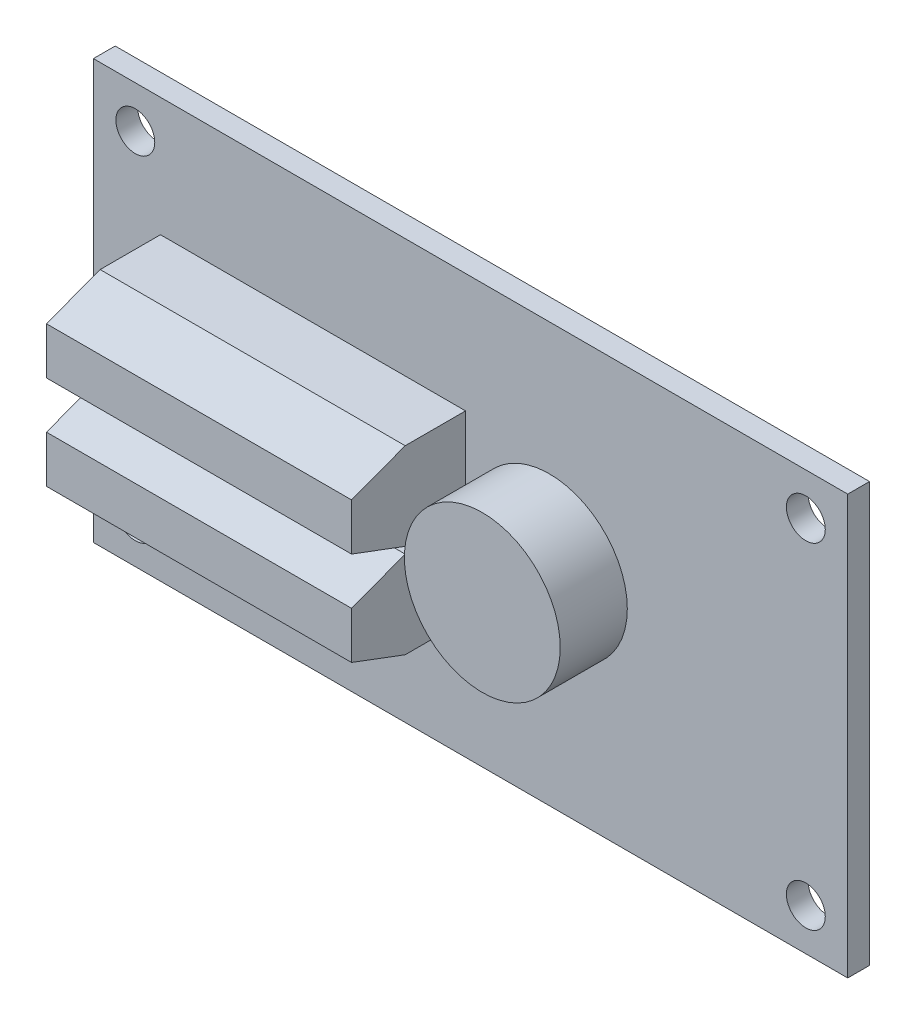
SolidWorks part; units mm, degrees
ref_plane "Front Plane" through (0, 0, 0) normal (0, 0, 1) x (1, 0, 0)
ref_plane "Top Plane" through (0, 0, 0) normal (0, 1, 0) x (1, 0, 0)
ref_plane "Right Plane" through (0, 0, 0) normal (1, 0, 0) x (0, 0, -1)
sketch "Sketch1" plane through (0, 0, 0) normal (0, 0, 1) x (1, 0, 0)
  line L1 (-28.575, 15.875) -> (28.575, 15.875)
  line L2 (-28.575, 15.875) -> (-28.575, -15.875)
  line L3 (-28.575, -15.875) -> (28.575, -15.875)
  line L4 (28.575, 15.875) -> (28.575, -15.875)
  line L5 (-28.575, 15.875) -> (28.575, -15.875) construction
  line L6 (-28.575, -15.875) -> (28.575, 15.875) construction
  point P0 (0, 0)
  dimension "D1" = 57.15
  dimension "D2" = 31.75
extrude "Boss-Extrude1" add sketch "Sketch1" along normal blind 1.651
sketch "Sketch2" plane through (0, 0, 1.651) normal (0, 0, 1) x (1, 0, 0)
  line L0 (25.4, 15.875) -> (25.4, -15.875) construction
  line L1 (28.575, 15.875) -> (-28.575, 15.875) construction
  line L2 (-28.575, -15.875) -> (28.575, -15.875) construction
  line L3 (-25.4, 15.875) -> (-25.4, -15.875) construction
  line L4 (-28.575, 12.7) -> (28.575, 12.7) construction
  line L5 (-28.575, 15.875) -> (-28.575, -15.875) construction
  line L6 (28.575, -15.875) -> (28.575, 15.875) construction
  line L7 (-28.575, -12.7) -> (28.575, -12.7) construction
  circle A0 centre (25.4, -12.7) radius 1.4732
  circle A1 centre (25.4, 12.7) radius 1.4732
  circle A2 centre (-25.4, 12.7) radius 1.4732
  circle A3 centre (-25.4, -12.7) radius 1.4732
  dimension "D1" = 2.9464
  dimension "D2" = 3.175
  dimension "D3" = 3.175
  dimension "D4" = 3.175
  dimension "D5" = 3.175
extrude "Mount-Holes" cut sketch "Sketch2" against normal through all
sketch "Sketch3" plane through (0, 0, 1.651) normal (0, 0, 1) x (1, 0, 0)
  line L0 (0, 0) -> (-28.575, 0) construction
  line L1 (-28.575, 15.875) -> (-28.575, -15.875) construction
  line L3 (-23.495, -0.254) -> (-0.381, -0.254)
  line L4 (-23.495, -0.254) -> (-23.495, -6.858)
  line L5 (-23.495, -6.858) -> (-0.381, -6.858)
  line L6 (-0.381, -0.254) -> (-0.381, -6.858)
  dimension "D1" = 6.604
  dimension "D2" = 23.114
  dimension "D3" = 5.08
  dimension "D4" = 0.254
extrude "Boss-Extrude2" add sketch "Sketch3" along normal blind 8.636
sketch "Sketch4" plane through (-23.495, 0, 0) normal (-1, 0, 0) x (0, 0, 1)
  line L0 (6.223, -6.858) -> (10.287, -5.334)
  line L1 (10.287, -6.858) -> (1.651, -6.858) construction
  line L2 (10.287, -0.254) -> (10.287, -6.858) construction
  line L3 (6.223, -6.858) -> (10.287, -6.858)
  line L4 (10.287, -6.858) -> (10.287, -5.334)
  line L5 (10.287, -3.556) -> (6.223, -3.556) construction
  line L6 (10.287, -0.254) -> (10.287, -1.778)
  line L7 (6.223, -0.254) -> (10.287, -0.254)
  line L8 (6.223, -0.254) -> (10.287, -1.778)
  dimension "D1" = 4.064
  dimension "D2" = 1.524
extrude "Cut-Extrude1" cut sketch "Sketch4" against normal up to next (23.114 mm away)
mirror "Mirror1" about plane through (0, 0, 0) normal (0, 1, 0) of "Cut-Extrude1", "Boss-Extrude2"
sketch "Sketch5" plane through (0, 0, 0) normal (0, 0, -1) x (-1, 0, 0)
  line L1 (-20.193, 4.953) -> (-10.287, 4.953)
  line L2 (-20.193, 4.953) -> (-20.193, -4.953)
  line L3 (-20.193, -4.953) -> (-10.287, -4.953)
  line L4 (-10.287, 4.953) -> (-10.287, -4.953)
  line L5 (-28.575, -15.875) -> (-28.575, 15.875) construction
  line L6 (-28.575, 0) -> (-24.0213, 0) construction
  point P9 (-20.193, 0)
  dimension "D1" = 9.906
  dimension "D3" = 8.382
extrude "Large bottom chip" add sketch "Sketch5" along normal blind 1.524
sketch "Sketch8" plane through (0, 0, 1.651) normal (0, 0, 1) x (1, 0, 0)
  line L0 (-28.575, 0) -> (1.7823, 0) construction
  line L1 (-28.575, 15.875) -> (-28.575, -15.875) construction
  line L2 (-0.381, -5.334) -> (-0.381, -1.778) construction
  circle A0 centre (5.969, 0) radius 5.9055
  dimension "D1" = 11.811
  dimension "D2" = 6.35
extrude "Buzzer" add sketch "Sketch8" along normal blind 5.08
sketch "Sketch9" plane through (0, 0, 0) normal (0, 0, -1) x (-1, 0, 0)
  line L0 (28.575, -15.875) -> (-28.575, -15.875) construction
  line L1 (-4.445, -9.906) -> (3.175, -9.906)
  line L2 (-4.445, -9.906) -> (-4.445, -15.748)
  line L3 (-4.445, -15.748) -> (3.175, -15.748)
  line L4 (3.175, -9.906) -> (3.175, -15.748)
  line L5 (-28.575, -15.875) -> (-28.575, 15.875) construction
  dimension "D1" = 7.62
  dimension "D2" = 5.842
  dimension "D3" = 0.127
  dimension "D4" = 24.13
extrude "USB Connector" add sketch "Sketch9" along normal blind 2.54
equation "\"D2@Sketch8\"=0.25"
